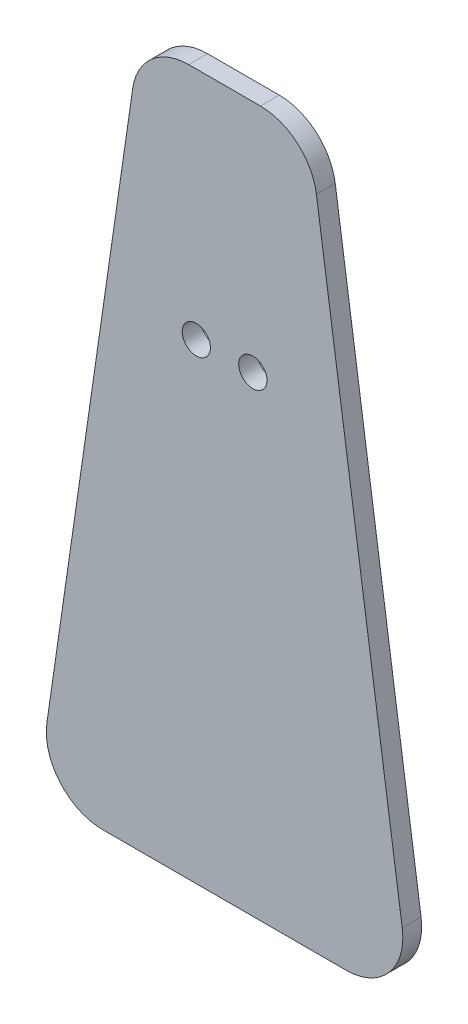
SolidWorks part; units mm, degrees
ref_plane "Front" through (0, 0, 0) normal (0, 0, 1) x (1, 0, 0)
ref_plane "Top" through (0, 0, 0) normal (0, 1, 0) x (1, 0, 0)
ref_plane "Right" through (0, 0, 0) normal (1, 0, 0) x (0, 0, -1)
sketch "草图1" plane through (0, 0, 0) normal (0, 0, 1) x (1, 0, 0)
  line L9 (-12.9172, 0) -> (12.9172, 0)
  line L16 (0, 74.8779) -> (3.8067, 74.8779)
  line L18 (0, 74.8779) -> (-3.8067, 74.8779)
  line L19 (-9.7447, 69.7383) -> (-18.8552, 6.8604)
  line L20 (9.7447, 69.7383) -> (18.8552, 6.8604)
  arc A2 (12.9172, 0) -> (18.8552, 6.8604) centre (12.9172, 6) ccw
  arc A3 (-18.8552, 6.8604) -> (-12.9172, 0) centre (-12.9172, 6) ccw
  arc A4 (-9.7447, 69.7383) -> (-3.8067, 74.8779) centre (-3.8067, 68.8779) cw
  arc A5 (9.7447, 69.7383) -> (3.8067, 74.8779) centre (3.8067, 68.8779) ccw
  circle A6 centre (-3, 50) radius 1.5
  circle A7 centre (3, 50) radius 1.5
  point P0 (0, 74.8779)
  dimension "D1" = 6
  dimension "D2" = 6
  dimension "D6" = 6
  dimension "D8" = 6
  dimension "D9" = 3
  dimension "D10" = 3
  dimension "D11" = 50
  dimension "D12" = 50
extrude "凸台-拉伸1" add sketch "草图1" along normal blind 2
